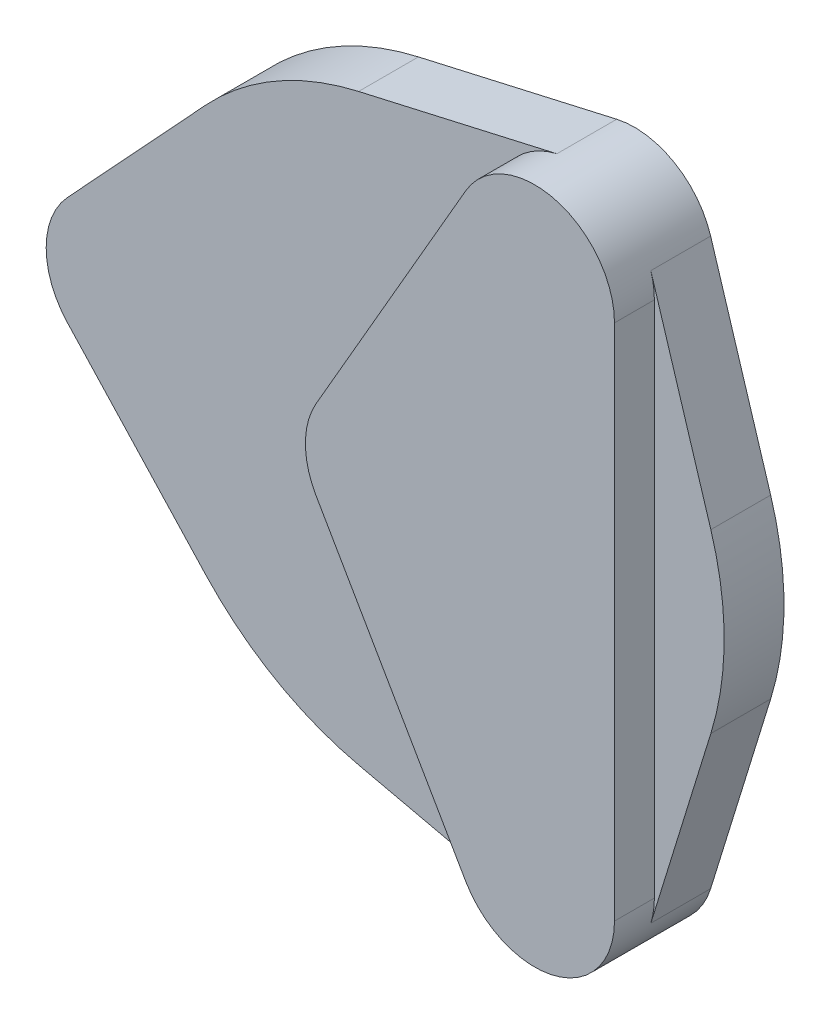
SolidWorks part; units mm, degrees
ref_plane "前基準面" through (0, 0, 0) normal (0, 0, 1) x (1, 0, 0)
ref_plane "上基準面" through (0, 0, 0) normal (0, 1, 0) x (1, 0, 0)
ref_plane "右基準面" through (0, 0, 0) normal (1, 0, 0) x (0, 0, -1)
sketch "草圖1" plane through (0, 0, 0) normal (0, 0, 1) x (1, 0, 0)
  line L0 (-22, 20.3961) -> (-35.8667, 5.439)
  line L1 (-35.8667, -5.439) -> (-22, -20.3961)
  line L2 (-6.6635, -29.2506) -> (13.2231, -33.7809)
  line L3 (22.6436, -28.342) -> (28.6635, -8.8545)
  line L4 (28.6635, 8.8545) -> (22.6436, 28.342)
  line L5 (13.2231, 33.7809) -> (-6.6635, 29.2506)
  line L7 (15, 25.9808) -> (-30, 0) construction
  line L8 (-30, 0) -> (15, -25.9808) construction
  line L9 (15, -25.9808) -> (15, 25.9808) construction
  circle A0 centre (0, 0) radius 30 construction
  arc A1 (-35.8667, -5.439) -> (-35.8667, 5.439) centre (-30, 0) cw
  arc A2 (13.2231, 33.7809) -> (22.6436, 28.342) centre (15, 25.9808) cw
  arc A3 (22.6436, -28.342) -> (13.2231, -33.7809) centre (15, -25.9808) cw
  arc A4 (-22, -20.3961) -> (-6.6635, -29.2506) centre (0, 0) ccw
  arc A5 (28.6635, -8.8545) -> (28.6635, 8.8545) centre (0, 0) ccw
  arc A6 (-22, 20.3961) -> (-6.6635, 29.2506) centre (0, 0) cw
  circle A7 centre (0, 0) radius 15 construction
  dimension "D1" = 60
  dimension "D2" = 8
  dimension "D3" = 8
  dimension "D4" = 8
extrude "填料-伸長1" add sketch "草圖1" along normal blind 6
sketch "草圖3" plane through (0, 0, 0) normal (0, 0, 1) x (1, 0, 0)
  line L0 (8.0718, 29.9808) -> (-6.9282, 4)
  line L1 (-6.9282, -4) -> (8.0718, -29.9808)
  line L2 (23, 25.9808) -> (23, -25.9808)
  arc A0 (-6.9282, -4) -> (-6.9282, 4) centre (0, 0) cw
  arc A1 (8.0718, 29.9808) -> (23, 25.9808) centre (15, 25.9808) cw
  arc A2 (22.6436, 28.342) -> (13.2231, 33.7809) centre (15, 25.9808) ccw construction
  arc A3 (23, -25.9808) -> (8.0718, -29.9808) centre (15, -25.9808) cw
  arc A4 (13.2231, -33.7809) -> (22.6436, -28.342) centre (15, -25.9808) ccw construction
  dimension "D1" = 8
extrude "填料-伸長2" add sketch "草圖3" along normal blind 10
